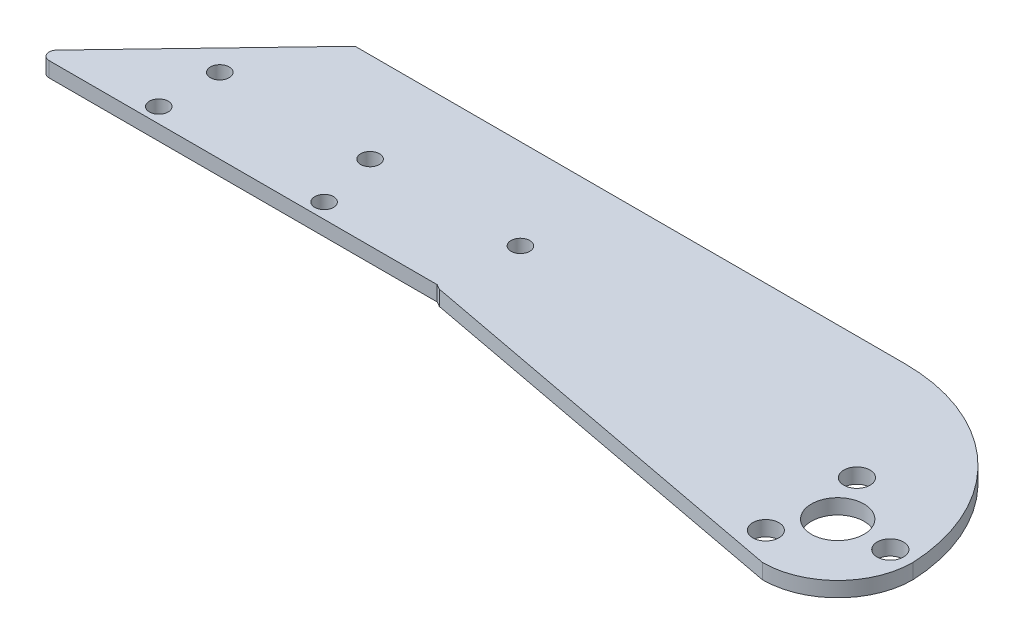
SolidWorks part; units mm, degrees
ref_plane "Спереди" through (0, 0, 0) normal (0, 0, 1) x (1, 0, 0)
ref_plane "Сверху" through (0, 0, 0) normal (0, 1, 0) x (1, 0, 0)
ref_plane "Справа" through (0, 0, 0) normal (1, 0, 0) x (0, 0, -1)
sketch "Sketch1" plane through (0, 0, 0) normal (0, 1, 0) x (1, 0, 0)
  line L0 (-69.9774, 22.3839) -> (-13.4172, 22.3839)
  line L1 (-108, 0) -> (0, 0) construction
  line L2 (0, -10) -> (0, 10)
  line L3 (-102.9617, -0.614) -> (-80.9617, -0.614) construction
  line L4 (-102.9617, -0.614) -> (-102.9617, 5.2684) construction
  line L5 (-108, 0) -> (-86.5935, 22.3839) construction
  line L6 (-86.5935, 22.3839) -> (-69.9774, 22.3839)
  line L7 (-53, 0) -> (-53.6615, 0.375)
  line L8 (0, -10) -> (-53, 0)
  line L9 (-102.9617, 5.2684) -> (-80.9617, 5.2684) construction
  line L10 (-80.9617, -0.614) -> (-80.9617, 5.2684) construction
  line L11 (-53.6615, 0.375) -> (-107.6414, 0.375)
  line L12 (-107.6414, 0.375) -> (-86.5935, 22.3839)
  line L13 (-80.9617, 5.2684) -> (-59.7052, 5.2684) construction
  line L14 (-80.9617, 5.2684) -> (-80.9617, -16.7229) construction
  line L15 (-80.9617, -16.7229) -> (-59.7052, -16.7229) construction
  line L16 (-59.7052, 5.2684) -> (-59.7052, -16.7229) construction
  circle A0 centre (0, 0) radius 10 construction
  circle A1 centre (-92.7052, 2.375) radius 1.25
  circle A2 centre (-70.7052, 2.375) radius 1.25
  circle A3 centre (0, 0) radius 7 construction
  circle A4 centre (7, 0) radius 1.75
  circle A5 centre (-3.5, -6.0622) radius 1.75
  circle A6 centre (-3.5, 6.0622) radius 1.75
  circle A7 centre (0, 0) radius 3.5
  arc A8 (0, -10) -> (0, 10) centre (0, 0) ccw
  arc A9 (-13.4172, 22.3839) -> (10, 0) centre (-13.4172, -1.0571) cw
  arc A10 (0, -10) -> (10, 0) centre (0, 0) ccw
  point P23 (0, 0)
  point P29 (-102.9617, 2.3272)
  point P30 (-59.7052, -5.7273)
  dimension "D1" = 20
  dimension "D3" = 22
  dimension "D5" = 2.5
  dimension "D6" = 3
  dimension "D7" = 14
  dimension "D8" = 3.5
  dimension "D9" = 7
  dimension "D10" = 44
  dimension "D13" = 2.5
  dimension "D2" = 108
  dimension "D4" = 53
  dimension "D11" = 2
  dimension "D12" = 0.75
extrude "Boss-Extrude1" add sketch "Sketch1" along normal blind 2 contours A9 L0 L6 L12 L11 L7 L8 L2 A7 A8 A6 A5 A2 A1 | A9 A8 L2 A7 A4
fillet "Скругление1" radius 1 1 edges at (-107.6414, 1, -0.375)
sketch "Эскиз1" plane through (0, 2, 0) normal (0, 1, 0) x (1, 0, 0)
  line L0 (-52.5935, 10.375) -> (-92.5935, 10.375) construction
  line L1 (-53.6615, 0.375) -> (-105.3014, 0.375) construction
  circle A0 centre (-92.5935, 10.375) radius 1.25
  circle A1 centre (-72.5935, 10.375) radius 1.25
  circle A2 centre (-52.5935, 10.375) radius 1.25
  point P8 (-79.4814, 0.375)
  point P9 (-92.8229, 10.375)
  dimension "D2" = 2.5
  dimension "D1" = 40
  dimension "D3" = 10
  dimension "D4" = 6
extrude "Вырез-Вытянуть1" cut sketch "Эскиз1" against normal through all both and the other way through all
